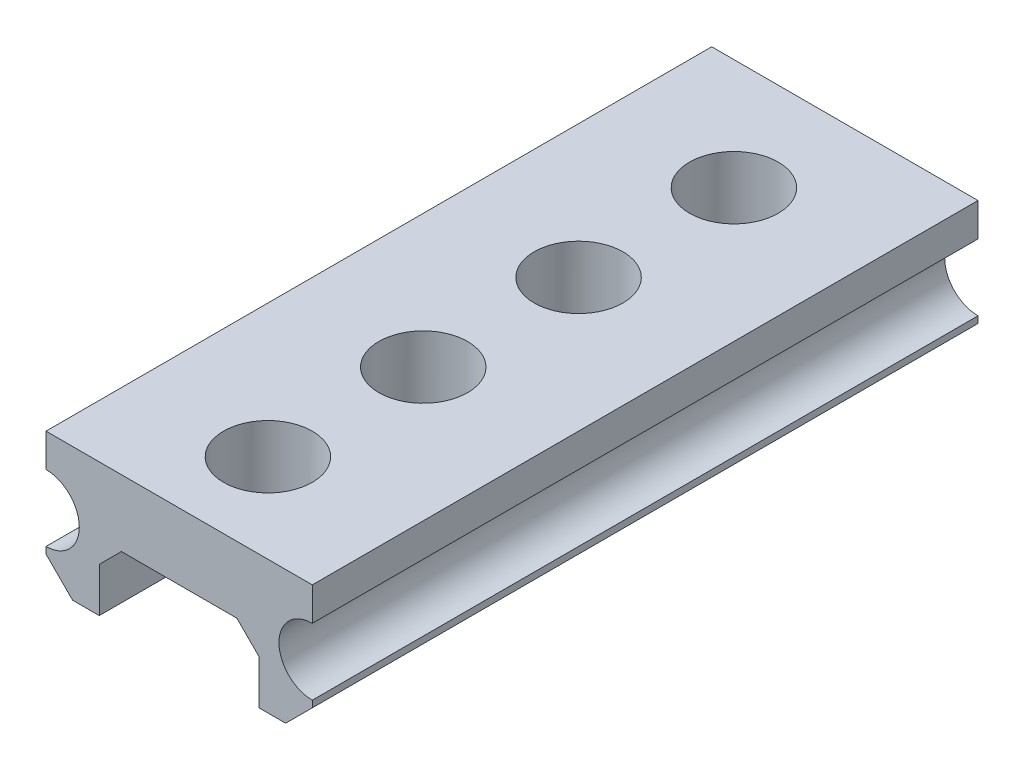
SolidWorks part; units mm, degrees
material "Nickel"
ref_plane "Front Plane" through (0, 0, 0) normal (0, 0, 1) x (1, 0, 0)
ref_plane "Top Plane" through (0, 0, 0) normal (0, 1, 0) x (1, 0, 0)
ref_plane "Right Plane" through (0, 0, 0) normal (1, 0, 0) x (0, 0, -1)
sketch "Sketch1" plane through (0, 0, 0) normal (0, 0, 1) x (1, 0, 0)
  line L1 (-3, 1.5) -> (3, 1.5)
  line L2 (-3, 1.5) -> (-3, -1.5)
  line L3 (-3, -1.5) -> (3, -1.5)
  line L4 (3, 1.5) -> (3, -1.5)
  line L5 (-3, 1.5) -> (3, -1.5) construction
  line L6 (-3, -1.5) -> (3, 1.5) construction
  dimension "D1" = 6
  dimension "D2" = 3
extrude "Boss-Extrude1" add sketch "Sketch1" along normal blind 15
sketch "Sketch2" plane through (0, 0, 15) normal (0, 0, 1) x (1, 0, 0)
  line L0 (3, -1.5) -> (3, 1.5) construction
  line L1 (-3, 1.5) -> (-3, -1.5) construction
  circle A0 centre (3, 0) radius 0.75
  circle A1 centre (-3, 0) radius 0.75
  dimension "D1" = 1.5
  dimension "D2" = 1.5
extrude "Cut-Extrude1" cut sketch "Sketch2" against normal blind 20
chamfer "Chamfer1" distance 0.6 angle 45 2 edges at (-3, -1.5, 7.5) (3, -1.5, 7.5)
sketch "Sketch3" plane through (0, 1.5, 0) normal (0, 1, 0) x (1, 0, 0)
  line L0 (0, 0) -> (0, -2.5) construction
  circle A0 centre (0, -2.5) radius 1
  dimension "D1" = 2
  dimension "D2" = 2.5
extrude "Cut-Extrude2" cut sketch "Sketch3" against normal blind 20
pattern_linear "LPattern1" count 4 spacing 3.5 along (0, 0, 1) of "Cut-Extrude2"
sketch "Sketch4" plane through (0, 0, 0) normal (0, 0, -1) x (-1, 0, 0)
  line L0 (1.8, -1.5) -> (1.8, 0)
  line L1 (2.4, -1.5) -> (-2.4, -1.5) construction
  line L2 (1.8, 0) -> (-1.8, 0)
  line L3 (-1.8, 0) -> (-1.8, -1.5)
  line L4 (-1.8, -1.5) -> (1.8, -1.5)
  line L5 (0, 0) -> (0, -1.5) construction
  line L6 (3, -0.75) -> (3, -0.9) construction
  line L7 (-3, 1.5) -> (3, 1.5) construction
  dimension "D1" = 1.2
  dimension "D2" = 1.5
extrude "Cut-Extrude3" cut sketch "Sketch4" against normal blind 20
chamfer "Chamfer2" distance 0.5 angle 45 2 edges at (1.8, 0, 7.5) (-1.8, 0, 7.5)
